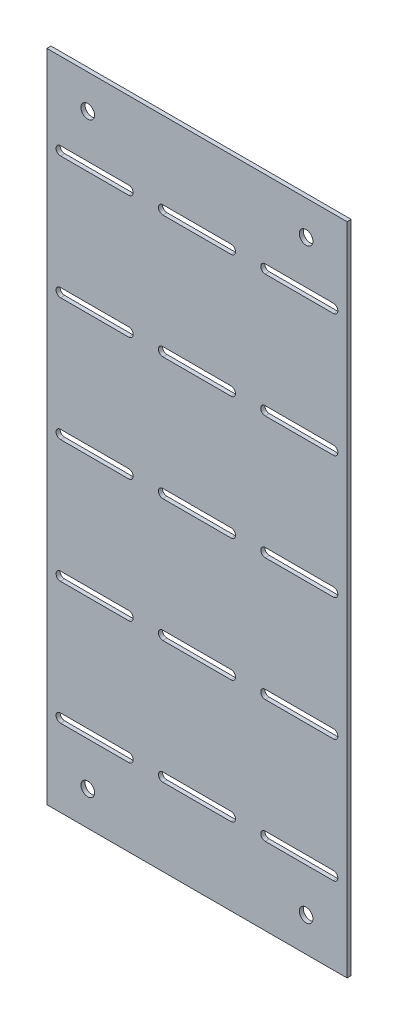
SolidWorks part; units mm, degrees
ref_plane "Alzado" through (0, 0, 0) normal (0, 0, 1) x (1, 0, 0)
ref_plane "Planta" through (0, 0, 0) normal (0, 1, 0) x (1, 0, 0)
ref_plane "Vista lateral" through (0, 0, 0) normal (1, 0, 0) x (0, 0, -1)
sketch "Croquis1" plane through (0, 0, 0) normal (0, 0, 1) x (1, 0, 0)
  line L1 (-110, 240) -> (110, 240)
  line L2 (-110, 240) -> (-110, -240)
  line L3 (-110, -240) -> (110, -240)
  line L4 (110, 240) -> (110, -240)
  line L5 (-110, 240) -> (110, -240) construction
  line L6 (-110, -240) -> (110, 240) construction
  point P0 (0, 0)
  dimension "D1" = 480
  dimension "D2" = 220
extrude "Saliente-Extruir1" add sketch "Croquis1" along normal blind 3
sketch "Croquis2" plane through (0, 0, 0) normal (0, 0, -1) x (-1, 0, 0)
  line L0 (-100, 90) -> (-100, 0) construction
  line L4 (-100, 0) -> (-50, 0) construction
  line L5 (-100, 3.25) -> (-50, 3.25)
  line L6 (-100, -3.25) -> (-50, -3.25)
  line L7 (-100, 90) -> (-50, 90) construction
  line L8 (-100, 93.25) -> (-50, 93.25)
  line L9 (-100, 86.75) -> (-50, 86.75)
  line L10 (0, 0) -> (53.7236, 0) construction
  line L11 (-100, -90) -> (-50, -90) construction
  line L12 (-100, -93.25) -> (-50, -93.25)
  line L13 (-100, -86.75) -> (-50, -86.75)
  line L14 (-25, 0) -> (25, 0) construction
  line L15 (-25, 3.25) -> (25, 3.25)
  line L16 (-25, -3.25) -> (25, -3.25)
  line L17 (-25, 90) -> (25, 90) construction
  line L18 (-25, 93.25) -> (25, 93.25)
  line L19 (-25, 86.75) -> (25, 86.75)
  line L20 (-25, -90) -> (25, -90) construction
  line L21 (-25, -93.25) -> (25, -93.25)
  line L22 (-25, -86.75) -> (25, -86.75)
  line L23 (50, 0) -> (100, 0) construction
  line L24 (50, 3.25) -> (100, 3.25)
  line L25 (50, -3.25) -> (100, -3.25)
  line L26 (50, 90) -> (100, 90) construction
  line L27 (50, 93.25) -> (100, 93.25)
  line L28 (50, 86.75) -> (100, 86.75)
  line L29 (50, -90) -> (100, -90) construction
  line L30 (50, -93.25) -> (100, -93.25)
  line L31 (50, -86.75) -> (100, -86.75)
  line L32 (-100, 90) -> (-25, 90) construction
  line L33 (-100, 90) -> (-100, 180) construction
  line L34 (-100, 180) -> (-50, 180) construction
  line L35 (-100, 183.25) -> (-50, 183.25)
  line L36 (-100, 176.75) -> (-50, 176.75)
  line L37 (-25, 180) -> (25, 180) construction
  line L38 (-25, 183.25) -> (25, 183.25)
  line L39 (-25, 176.75) -> (25, 176.75)
  line L40 (50, 180) -> (100, 180) construction
  line L41 (50, 183.25) -> (100, 183.25)
  line L42 (50, 176.75) -> (100, 176.75)
  line L43 (-100, 180) -> (-25, 180) construction
  line L44 (-100, -180) -> (-50, -180) construction
  line L45 (-100, -183.25) -> (-50, -183.25)
  line L46 (-100, -176.75) -> (-50, -176.75)
  line L47 (-25, -180) -> (25, -180) construction
  line L48 (-25, -183.25) -> (25, -183.25)
  line L49 (-25, -176.75) -> (25, -176.75)
  line L50 (50, -180) -> (100, -180) construction
  line L51 (50, -183.25) -> (100, -183.25)
  line L52 (50, -176.75) -> (100, -176.75)
  circle A1 centre (-80, 215) radius 5
  circle A2 centre (-80, 215) radius 5
  circle A3 centre (80, 215) radius 5
  circle A4 centre (80, 215) radius 5
  circle A5 centre (80, -215) radius 5
  circle A6 centre (80, -215) radius 5
  circle A7 centre (-80, -215) radius 5
  circle A8 centre (-80, -215) radius 5
  arc A10 (-100, 3.25) -> (-100, -3.25) centre (-100, 0) ccw
  arc A11 (-50, -3.25) -> (-50, 3.25) centre (-50, 0) ccw
  arc A12 (-100, 93.25) -> (-100, 86.75) centre (-100, 90) ccw
  arc A13 (-50, 86.75) -> (-50, 93.25) centre (-50, 90) ccw
  arc A14 (-100, -93.25) -> (-100, -86.75) centre (-100, -90) cw
  arc A15 (-50, -86.75) -> (-50, -93.25) centre (-50, -90) cw
  arc A16 (-25, 3.25) -> (-25, -3.25) centre (-25, 0) ccw
  arc A17 (25, -3.25) -> (25, 3.25) centre (25, 0) ccw
  arc A18 (-25, 93.25) -> (-25, 86.75) centre (-25, 90) ccw
  arc A19 (25, 86.75) -> (25, 93.25) centre (25, 90) ccw
  arc A20 (-25, -93.25) -> (-25, -86.75) centre (-25, -90) cw
  arc A21 (25, -86.75) -> (25, -93.25) centre (25, -90) cw
  arc A22 (50, 3.25) -> (50, -3.25) centre (50, 0) ccw
  arc A23 (100, -3.25) -> (100, 3.25) centre (100, 0) ccw
  arc A24 (50, 93.25) -> (50, 86.75) centre (50, 90) ccw
  arc A25 (100, 86.75) -> (100, 93.25) centre (100, 90) ccw
  arc A26 (50, -93.25) -> (50, -86.75) centre (50, -90) cw
  arc A27 (100, -86.75) -> (100, -93.25) centre (100, -90) cw
  arc A52 (-100, 183.25) -> (-100, 176.75) centre (-100, 180) ccw
  arc A53 (-50, 176.75) -> (-50, 183.25) centre (-50, 180) ccw
  arc A54 (-25, 183.25) -> (-25, 176.75) centre (-25, 180) ccw
  arc A55 (25, 176.75) -> (25, 183.25) centre (25, 180) ccw
  arc A56 (50, 183.25) -> (50, 176.75) centre (50, 180) ccw
  arc A57 (100, 176.75) -> (100, 183.25) centre (100, 180) ccw
  arc A58 (-100, -183.25) -> (-100, -176.75) centre (-100, -180) cw
  arc A59 (-50, -176.75) -> (-50, -183.25) centre (-50, -180) cw
  arc A60 (-25, -183.25) -> (-25, -176.75) centre (-25, -180) cw
  arc A61 (25, -176.75) -> (25, -183.25) centre (25, -180) cw
  arc A62 (50, -183.25) -> (50, -176.75) centre (50, -180) cw
  arc A63 (100, -176.75) -> (100, -183.25) centre (100, -180) cw
  point P0 (-75, 180)
  point P16 (-75, 90)
  point P21 (-75, 0)
  point P37 (-75, -90)
  point P44 (0, 90)
  point P49 (0, 0)
  point P60 (0, -90)
  point P65 (75, 90)
  point P70 (75, 0)
  point P81 (75, -90)
  point P92 (0, 180)
  point P99 (75, 180)
  point P108 (-75, -180)
  point P115 (0, -180)
  point P122 (75, -180)
  dimension "D5" = 100
  dimension "D6" = 50
  dimension "D7" = 6.5
  dimension "D8" = 50
  dimension "D9" = 6.5
  dimension "D11" = 75
  dimension "D12" = 90
  dimension "D13" = 90
  dimension "D14" = 50
  dimension "D15" = 6.5
  dimension "D17" = 75
  dimension "D1" = 0
  dimension "D2" = 0
  dimension "D3" = 0
  dimension "D4" = 0
  dimension "D10" = 3
  dimension "D16" = 3
extrude "Cortar-Extruir1" cut sketch "Croquis2" against normal blind 3
